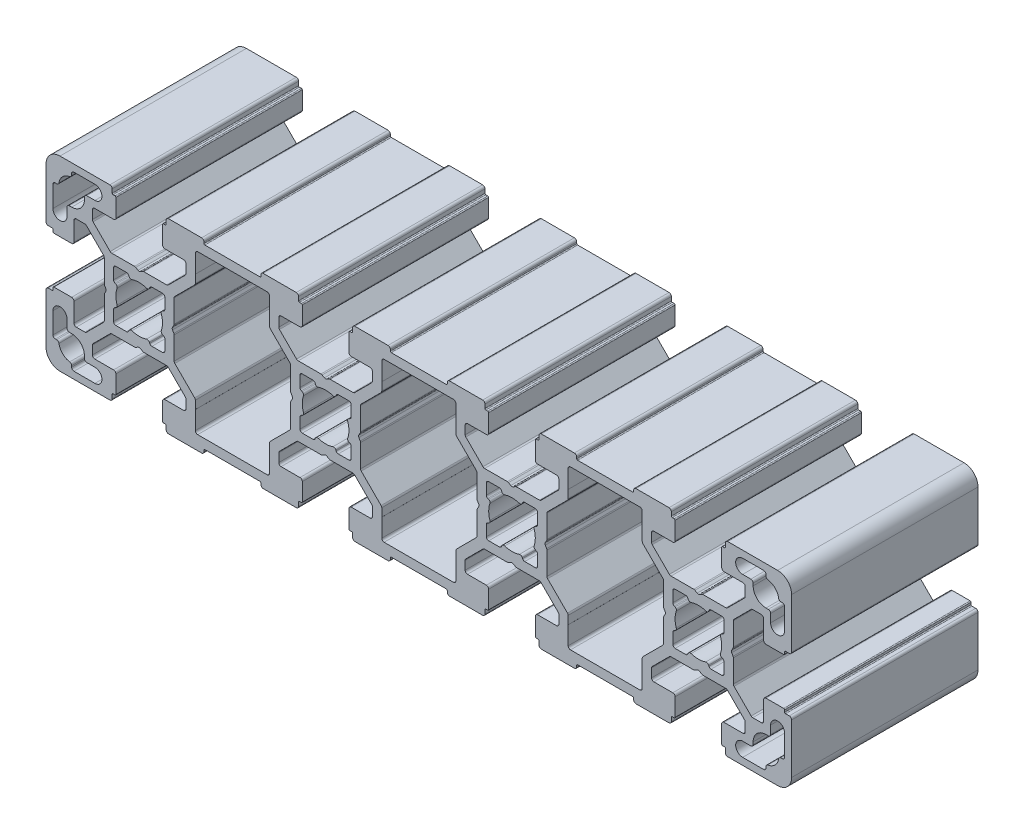
SolidWorks part; units mm, degrees
material "АД31Т ГОСТ 4784-97"
ref_plane "Спереди" through (0, 0, 0) normal (0, 0, 1) x (1, 0, 0)
ref_plane "Сверху" through (0, 0, 0) normal (0, 1, 0) x (1, 0, 0)
ref_plane "Справа" through (0, 0, 0) normal (1, 0, 0) x (0, 0, -1)
sketch "Эскиз1" plane through (0, 0, 0) normal (0, 0, 1) x (1, 0, 0)
  line B0 (-95.6887, 53.3596) -> (-95.6109, 53.5385)
  line B1 (-98.4194, 53.059) -> (-96.1473, 53.059)
  line B2 (-98.9194, 55.8312) -> (-98.9194, 53.559)
  line B3 (-98.4399, 56.3675) -> (-98.6188, 56.2897)
  line B4 (-98.6188, 60.8283) -> (-98.4399, 60.7505)
  line B5 (-98.9194, 63.559) -> (-98.9194, 61.2868)
  line B6 (-96.1473, 64.059) -> (-98.4194, 64.059)
  line B7 (-95.6109, 63.5795) -> (-95.6887, 63.7584)
  line B8 (-91.1502, 63.7584) -> (-91.2279, 63.5795)
  line B9 (-88.4194, 64.059) -> (-90.6916, 64.059)
  line B10 (-87.9194, 61.2868) -> (-87.9194, 63.559)
  line B11 (-88.399, 60.7505) -> (-88.2201, 60.8283)
  line B12 (-88.2201, 56.2897) -> (-88.399, 56.3675)
  line B13 (-87.9194, 53.559) -> (-87.9194, 55.8312)
  line B14 (-90.6916, 53.059) -> (-88.4194, 53.059)
  line B15 (-91.2279, 53.5385) -> (-91.1502, 53.3596)
  line B16 (-65.323, 48.0696) -> (-61.0659, 52.3267)
  line B17 (-65.4694, 45.9733) -> (-65.4694, 47.7161)
  line B18 (-65.4844, 45.9788) -> (-65.4694, 45.9733)
  line B19 (-65.4711, 42.0607) -> (-65.4844, 45.9788)
  line B20 (-80.8677, 41.559) -> (-65.9711, 41.559)
  line B21 (-81.3544, 45.9788) -> (-81.3677, 42.0607)
  line B22 (-81.3694, 45.9733) -> (-81.3544, 45.9788)
  line B23 (-81.3694, 47.7161) -> (-81.3694, 45.9733)
  line B24 (-85.773, 52.3267) -> (-81.5159, 48.0696)
  line B25 (-85.9194, 57.559) -> (-85.9194, 52.6803)
  line B26 (-86.2751, 58.309) -> (-85.9864, 57.809)
  line B27 (-85.9864, 59.309) -> (-86.2751, 58.809)
  line B28 (-85.9194, 64.4377) -> (-85.9194, 59.559)
  line B29 (-81.5159, 69.0483) -> (-85.773, 64.7912)
  line B30 (-81.3694, 71.1446) -> (-81.3694, 69.4019)
  line B31 (-81.3544, 71.1391) -> (-81.3694, 71.1446)
  line B32 (-81.3677, 75.0573) -> (-81.3544, 71.1391)
  line B33 (-65.9711, 75.559) -> (-80.8677, 75.559)
  line B34 (-65.4844, 71.1391) -> (-65.4711, 75.0573)
  line B35 (-65.4694, 71.1446) -> (-65.4844, 71.1391)
  line B36 (-65.4694, 69.4019) -> (-65.4694, 71.1446)
  line B37 (-61.0659, 64.7912) -> (-65.323, 69.0483)
  line B38 (-60.9194, 59.559) -> (-60.9194, 64.4377)
  line B39 (-60.5638, 58.809) -> (-60.8524, 59.309)
  line B40 (-60.8524, 57.809) -> (-60.5638, 58.309)
  line B41 (-60.9194, 52.6803) -> (-60.9194, 57.559)
  line B42 (-55.6887, 53.3596) -> (-55.6109, 53.5385)
  line B43 (-58.4194, 53.059) -> (-56.1473, 53.059)
  line B44 (-58.9194, 55.8312) -> (-58.9194, 53.559)
  line B45 (-58.4399, 56.3675) -> (-58.6188, 56.2897)
  line B46 (-58.6188, 60.8283) -> (-58.4399, 60.7505)
  line B47 (-58.9194, 63.559) -> (-58.9194, 61.2868)
  line B48 (-56.1473, 64.059) -> (-58.4194, 64.059)
  line B49 (-55.6109, 63.5795) -> (-55.6887, 63.7584)
  line B50 (-51.1502, 63.7584) -> (-51.2279, 63.5795)
  line B51 (-48.4194, 64.059) -> (-50.6916, 64.059)
  line B52 (-47.9194, 61.2868) -> (-47.9194, 63.559)
  line B53 (-48.399, 60.7505) -> (-48.2201, 60.8283)
  line B54 (-48.2201, 56.2897) -> (-48.399, 56.3675)
  line B55 (-47.9194, 53.559) -> (-47.9194, 55.8312)
  line B56 (-50.6916, 53.059) -> (-48.4194, 53.059)
  line B57 (-51.2279, 53.5385) -> (-51.1502, 53.3596)
  line B58 (-25.9711, 75.559) -> (-40.8677, 75.559)
  line B59 (-25.4844, 71.1391) -> (-25.4711, 75.0573)
  line B60 (-25.4694, 71.1446) -> (-25.4844, 71.1391)
  line B61 (-25.4694, 69.4019) -> (-25.4694, 71.1446)
  line B62 (-21.0659, 64.7912) -> (-25.323, 69.0483)
  line B63 (-20.9194, 59.559) -> (-20.9194, 64.4377)
  line B64 (-20.5638, 58.809) -> (-20.8524, 59.309)
  line B65 (-20.8524, 57.809) -> (-20.5638, 58.309)
  line B66 (-20.9194, 52.6803) -> (-20.9194, 57.559)
  line B67 (-25.323, 48.0696) -> (-21.0659, 52.3267)
  line B68 (-25.4694, 45.9733) -> (-25.4694, 47.7161)
  line B69 (-25.4844, 45.9788) -> (-25.4694, 45.9733)
  line B70 (-25.4711, 42.0607) -> (-25.4844, 45.9788)
  line B71 (-40.8677, 41.559) -> (-25.9711, 41.559)
  line B72 (-41.3544, 45.9788) -> (-41.3677, 42.0607)
  line B73 (-41.3694, 45.9733) -> (-41.3544, 45.9788)
  line B74 (-41.3694, 47.7161) -> (-41.3694, 45.9733)
  line B75 (-45.773, 52.3267) -> (-41.5159, 48.0696)
  line B76 (-45.9194, 57.559) -> (-45.9194, 52.6803)
  line B77 (-46.2751, 58.309) -> (-45.9864, 57.809)
  line B78 (-45.9864, 59.309) -> (-46.2751, 58.809)
  line B79 (-45.9194, 64.4377) -> (-45.9194, 59.559)
  line B80 (-41.5159, 69.0483) -> (-45.773, 64.7912)
  line B81 (-41.3694, 71.1446) -> (-41.3694, 69.4019)
  line B82 (-41.3544, 71.1391) -> (-41.3694, 71.1446)
  line B83 (-41.3677, 75.0573) -> (-41.3544, 71.1391)
  line B84 (-27.5094, 77.559) -> (-39.3294, 77.559)
  line B85 (-39.5294, 77.759) -> (-39.5294, 78.059)
  line B86 (-40.0294, 78.559) -> (-47.1194, 78.559)
  line B87 (-47.6194, 78.059) -> (-47.6194, 77.259)
  line B88 (-47.8194, 77.059) -> (-48.2194, 77.059)
  line B89 (-48.4194, 76.859) -> (-48.4194, 73.059)
  line B90 (-47.9194, 72.559) -> (-43.8694, 72.559)
  line B91 (-43.3694, 72.059) -> (-43.3694, 70.2303)
  line B92 (-43.5159, 69.8767) -> (-47.1872, 66.2054)
  line B93 (-47.5408, 66.059) -> (-52.4194, 66.059)
  line B94 (-52.6694, 65.992) -> (-53.1694, 65.7033)
  line B95 (-53.6694, 65.7033) -> (-54.1694, 65.992)
  line B96 (-54.4194, 66.059) -> (-59.2981, 66.059)
  line B97 (-59.6517, 66.2054) -> (-63.323, 69.8767)
  line B98 (-63.4694, 70.2303) -> (-63.4694, 72.059)
  line B99 (-62.9694, 72.559) -> (-58.9194, 72.559)
  line B100 (-58.4194, 73.059) -> (-58.4194, 76.859)
  line B101 (-58.6194, 77.059) -> (-59.0194, 77.059)
  line B102 (-59.2194, 77.259) -> (-59.2194, 78.059)
  line B103 (-59.7194, 78.559) -> (-66.8094, 78.559)
  line B104 (-67.3094, 78.059) -> (-67.3094, 77.759)
  line B105 (-67.5094, 77.559) -> (-79.3294, 77.559)
  line B106 (-79.5294, 77.759) -> (-79.5294, 78.059)
  line B107 (-80.0294, 78.559) -> (-87.1194, 78.559)
  line B108 (-87.6194, 78.059) -> (-87.6194, 77.259)
  line B109 (-87.8194, 77.059) -> (-88.2194, 77.059)
  line B110 (-88.4194, 76.859) -> (-88.4194, 73.059)
  line B111 (-87.9194, 72.559) -> (-83.8694, 72.559)
  line B112 (-83.3694, 72.059) -> (-83.3694, 70.2303)
  line B113 (-83.5159, 69.8767) -> (-87.1872, 66.2054)
  line B114 (-87.5408, 66.059) -> (-92.4194, 66.059)
  line B115 (-92.6694, 65.992) -> (-93.1694, 65.7033)
  line B116 (-93.6694, 65.7033) -> (-94.1694, 65.992)
  line B117 (-94.4194, 66.059) -> (-99.2981, 66.059)
  line B118 (-99.6517, 66.2054) -> (-103.323, 69.8767)
  line B119 (-103.4694, 70.2303) -> (-103.4694, 72.059)
  line B120 (-102.9694, 72.559) -> (-98.9194, 72.559)
  line B121 (-98.4194, 73.059) -> (-98.4194, 76.859)
  line B122 (-98.6194, 77.059) -> (-99.0194, 77.059)
  line B123 (-99.2194, 77.259) -> (-99.2194, 78.059)
  line B124 (-99.7194, 78.559) -> (-110.4194, 78.559)
  line B125 (-113.4194, 75.559) -> (-113.4194, 64.859)
  line B126 (-112.9194, 64.359) -> (-112.1194, 64.359)
  line B127 (-111.9194, 64.159) -> (-111.9194, 63.759)
  line B128 (-111.7194, 63.559) -> (-107.9194, 63.559)
  line B129 (-107.4194, 64.059) -> (-107.4194, 68.109)
  line B130 (-106.9194, 68.609) -> (-105.0908, 68.609)
  line B131 (-104.7372, 68.4625) -> (-101.0659, 64.7912)
  line B132 (-100.9194, 64.4377) -> (-100.9194, 59.559)
  line B133 (-100.8524, 59.309) -> (-100.5638, 58.809)
  line B134 (-100.5638, 58.309) -> (-100.8524, 57.809)
  line B135 (-100.9194, 57.559) -> (-100.9194, 52.6803)
  line B136 (-101.0659, 52.3267) -> (-104.7372, 48.6554)
  line B137 (-105.0908, 48.509) -> (-106.9194, 48.509)
  line B138 (-107.4194, 49.009) -> (-107.4194, 53.059)
  line B139 (-107.9194, 53.559) -> (-111.7194, 53.559)
  line B140 (-111.9194, 53.359) -> (-111.9194, 52.959)
  line B141 (-112.1194, 52.759) -> (-112.9194, 52.759)
  line B142 (-113.4194, 52.259) -> (-113.4194, 41.559)
  line B143 (-110.4194, 38.559) -> (-99.7194, 38.559)
  line B144 (-99.2194, 39.059) -> (-99.2194, 39.859)
  line B145 (-99.0194, 40.059) -> (-98.6194, 40.059)
  line B146 (-98.4194, 40.259) -> (-98.4194, 44.059)
  line B147 (-98.9194, 44.559) -> (-102.9694, 44.559)
  line B148 (-103.4694, 45.059) -> (-103.4694, 46.8877)
  line B149 (-103.323, 47.2412) -> (-99.6517, 50.9125)
  line B150 (-99.2981, 51.059) -> (-94.4194, 51.059)
  line B151 (-94.1694, 51.126) -> (-93.6694, 51.4146)
  line B152 (-93.1694, 51.4146) -> (-92.6694, 51.126)
  line B153 (-92.4194, 51.059) -> (-87.5408, 51.059)
  line B154 (-87.1872, 50.9125) -> (-83.5159, 47.2412)
  line B155 (-83.3694, 46.8877) -> (-83.3694, 45.059)
  line B156 (-83.8694, 44.559) -> (-87.9194, 44.559)
  line B157 (-88.4194, 44.059) -> (-88.4194, 40.259)
  line B158 (-88.2194, 40.059) -> (-87.8194, 40.059)
  line B159 (-87.6194, 39.859) -> (-87.6194, 39.059)
  line B160 (-87.1194, 38.559) -> (-80.0294, 38.559)
  line B161 (-79.5294, 39.059) -> (-79.5294, 39.359)
  line B162 (-79.3294, 39.559) -> (-67.5094, 39.559)
  line B163 (-67.3094, 39.359) -> (-67.3094, 39.059)
  line B164 (-66.8094, 38.559) -> (-59.7194, 38.559)
  line B165 (-59.2194, 39.059) -> (-59.2194, 39.859)
  line B166 (-59.0194, 40.059) -> (-58.6194, 40.059)
  line B167 (-58.4194, 40.259) -> (-58.4194, 44.059)
  line B168 (-58.9194, 44.559) -> (-62.9694, 44.559)
  line B169 (-63.4694, 45.059) -> (-63.4694, 46.8877)
  line B170 (-63.323, 47.2412) -> (-59.6517, 50.9125)
  line B171 (-59.2981, 51.059) -> (-54.4194, 51.059)
  line B172 (-54.1694, 51.126) -> (-53.6694, 51.4146)
  line B173 (-53.1694, 51.4146) -> (-52.6694, 51.126)
  line B174 (-52.4194, 51.059) -> (-47.5408, 51.059)
  line B175 (-47.1872, 50.9125) -> (-43.5159, 47.2412)
  line B176 (-43.3694, 46.8877) -> (-43.3694, 45.059)
  line B177 (-43.8694, 44.559) -> (-47.9194, 44.559)
  line B178 (-48.4194, 44.059) -> (-48.4194, 40.259)
  line B179 (-48.2194, 40.059) -> (-47.8194, 40.059)
  line B180 (-47.6194, 39.859) -> (-47.6194, 39.059)
  line B181 (-47.1194, 38.559) -> (-40.0294, 38.559)
  line B182 (-39.5294, 39.059) -> (-39.5294, 39.359)
  line B183 (-39.3294, 39.559) -> (-27.5094, 39.559)
  line B184 (-27.3094, 39.359) -> (-27.3094, 39.059)
  line B185 (-26.8094, 38.559) -> (-19.7194, 38.559)
  line B186 (-19.2194, 39.059) -> (-19.2194, 39.859)
  line B187 (-19.0194, 40.059) -> (-18.6194, 40.059)
  line B188 (-18.4194, 40.259) -> (-18.4194, 44.059)
  line B189 (-18.9194, 44.559) -> (-22.9694, 44.559)
  line B190 (-23.4694, 45.059) -> (-23.4694, 46.8877)
  line B191 (-23.323, 47.2412) -> (-19.6517, 50.9125)
  line B192 (-19.2981, 51.059) -> (-14.4194, 51.059)
  line B193 (-14.1694, 51.126) -> (-13.6694, 51.4146)
  line B194 (-13.1694, 51.4146) -> (-12.6694, 51.126)
  line B195 (-12.4194, 51.059) -> (-7.5408, 51.059)
  line B196 (-7.1872, 50.9125) -> (-3.5159, 47.2412)
  line B197 (-3.3694, 46.8877) -> (-3.3694, 45.059)
  line B198 (-3.8694, 44.559) -> (-7.9194, 44.559)
  line B199 (-8.4194, 44.059) -> (-8.4194, 40.259)
  line B200 (-8.2194, 40.059) -> (-7.8194, 40.059)
  line B201 (-7.6194, 39.859) -> (-7.6194, 39.059)
  line B202 (-7.1194, 38.559) -> (-0.0294, 38.559)
  line B203 (0.4706, 39.059) -> (0.4706, 39.359)
  line B204 (0.6706, 39.559) -> (12.4906, 39.559)
  line B205 (12.6906, 39.359) -> (12.6906, 39.059)
  line B206 (13.1906, 38.559) -> (20.2806, 38.559)
  line B207 (20.7806, 39.059) -> (20.7806, 39.859)
  line B208 (20.9806, 40.059) -> (21.3806, 40.059)
  line B209 (21.5806, 40.259) -> (21.5806, 44.059)
  line B210 (21.0806, 44.559) -> (17.0306, 44.559)
  line B211 (16.5306, 45.059) -> (16.5306, 46.8877)
  line B212 (16.677, 47.2412) -> (20.3483, 50.9125)
  line B213 (20.7019, 51.059) -> (25.5806, 51.059)
  line B214 (25.8306, 51.126) -> (26.3306, 51.4146)
  line B215 (26.8306, 51.4146) -> (27.3306, 51.126)
  line B216 (27.5806, 51.059) -> (32.4592, 51.059)
  line B217 (32.8128, 50.9125) -> (36.4841, 47.2412)
  line B218 (36.6306, 46.8877) -> (36.6306, 45.059)
  line B219 (36.1306, 44.559) -> (32.0806, 44.559)
  line B220 (31.5806, 44.059) -> (31.5806, 40.259)
  line B221 (31.7806, 40.059) -> (32.1806, 40.059)
  line B222 (32.3806, 39.859) -> (32.3806, 39.059)
  line B223 (32.8806, 38.559) -> (43.5806, 38.559)
  line B224 (46.5806, 41.559) -> (46.5806, 52.259)
  line B225 (46.0806, 52.759) -> (45.2806, 52.759)
  line B226 (45.0806, 52.959) -> (45.0806, 53.359)
  line B227 (44.8806, 53.559) -> (41.0806, 53.559)
  line B228 (40.5806, 53.059) -> (40.5806, 49.009)
  line B229 (40.0806, 48.509) -> (38.2519, 48.509)
  line B230 (37.8983, 48.6554) -> (34.227, 52.3267)
  line B231 (34.0806, 52.6803) -> (34.0806, 57.559)
  line B232 (34.0136, 57.809) -> (33.7249, 58.309)
  line B233 (33.7249, 58.809) -> (34.0136, 59.309)
  line B234 (34.0806, 59.559) -> (34.0806, 64.4377)
  line B235 (34.227, 64.7912) -> (37.8983, 68.4625)
  line B236 (38.2519, 68.609) -> (40.0806, 68.609)
  line B237 (40.5806, 68.109) -> (40.5806, 64.059)
  line B238 (41.0806, 63.559) -> (44.8806, 63.559)
  line B239 (45.0806, 63.759) -> (45.0806, 64.159)
  line B240 (45.2806, 64.359) -> (46.0806, 64.359)
  line B241 (46.5806, 64.859) -> (46.5806, 75.559)
  line B242 (43.5806, 78.559) -> (32.8806, 78.559)
  line B243 (32.3806, 78.059) -> (32.3806, 77.259)
  line B244 (32.1806, 77.059) -> (31.7806, 77.059)
  line B245 (31.5806, 76.859) -> (31.5806, 73.059)
  line B246 (32.0806, 72.559) -> (36.1306, 72.559)
  line B247 (36.6306, 72.059) -> (36.6306, 70.2303)
  line B248 (36.4841, 69.8767) -> (32.8128, 66.2054)
  line B249 (32.4592, 66.059) -> (27.5806, 66.059)
  line B250 (27.3306, 65.992) -> (26.8306, 65.7033)
  line B251 (26.3306, 65.7033) -> (25.8306, 65.992)
  line B252 (25.5806, 66.059) -> (20.7019, 66.059)
  line B253 (20.3483, 66.2054) -> (16.677, 69.8767)
  line B254 (16.5306, 70.2303) -> (16.5306, 72.059)
  line B255 (17.0306, 72.559) -> (21.0806, 72.559)
  line B256 (21.5806, 73.059) -> (21.5806, 76.859)
  line B257 (21.3806, 77.059) -> (20.9806, 77.059)
  line B258 (20.7806, 77.259) -> (20.7806, 78.059)
  line B259 (20.2806, 78.559) -> (13.1906, 78.559)
  line B260 (12.6906, 78.059) -> (12.6906, 77.759)
  line B261 (12.4906, 77.559) -> (0.6706, 77.559)
  line B262 (0.4706, 77.759) -> (0.4706, 78.059)
  line B263 (-0.0294, 78.559) -> (-7.1194, 78.559)
  line B264 (-7.6194, 78.059) -> (-7.6194, 77.259)
  line B265 (-7.8194, 77.059) -> (-8.2194, 77.059)
  line B266 (-8.4194, 76.859) -> (-8.4194, 73.059)
  line B267 (-7.9194, 72.559) -> (-3.8694, 72.559)
  line B268 (-3.3694, 72.059) -> (-3.3694, 70.2303)
  line B269 (-3.5159, 69.8767) -> (-7.1872, 66.2054)
  line B270 (-7.5408, 66.059) -> (-12.4194, 66.059)
  line B271 (-12.6694, 65.992) -> (-13.1694, 65.7033)
  line B272 (-13.6694, 65.7033) -> (-14.1694, 65.992)
  line B273 (-14.4194, 66.059) -> (-19.2981, 66.059)
  line B274 (-19.6517, 66.2054) -> (-23.323, 69.8767)
  line B275 (-23.4694, 70.2303) -> (-23.4694, 72.059)
  line B276 (-22.9694, 72.559) -> (-18.9194, 72.559)
  line B277 (-18.4194, 73.059) -> (-18.4194, 76.859)
  line B278 (-18.6194, 77.059) -> (-19.0194, 77.059)
  line B279 (-19.2194, 77.259) -> (-19.2194, 78.059)
  line B280 (-19.7194, 78.559) -> (-26.8094, 78.559)
  line B281 (-27.3094, 78.059) -> (-27.3094, 77.759)
  line B282 (-11.1502, 63.7584) -> (-11.2279, 63.5795)
  line B283 (-8.4194, 64.059) -> (-10.6916, 64.059)
  line B284 (-7.9194, 61.2868) -> (-7.9194, 63.559)
  line B285 (-8.399, 60.7505) -> (-8.2201, 60.8283)
  line B286 (-8.2201, 56.2897) -> (-8.399, 56.3675)
  line B287 (-7.9194, 53.559) -> (-7.9194, 55.8312)
  line B288 (-10.6916, 53.059) -> (-8.4194, 53.059)
  line B289 (-11.2279, 53.5385) -> (-11.1502, 53.3596)
  line B290 (-15.6887, 53.3596) -> (-15.6109, 53.5385)
  line B291 (-18.4194, 53.059) -> (-16.1473, 53.059)
  line B292 (-18.9194, 55.8312) -> (-18.9194, 53.559)
  line B293 (-18.4399, 56.3675) -> (-18.6188, 56.2897)
  line B294 (-18.6188, 60.8283) -> (-18.4399, 60.7505)
  line B295 (-18.9194, 63.559) -> (-18.9194, 61.2868)
  line B296 (-16.1473, 64.059) -> (-18.4194, 64.059)
  line B297 (-15.6109, 63.5795) -> (-15.6887, 63.7584)
  line B298 (14.677, 48.0696) -> (18.9341, 52.3267)
  line B299 (14.5306, 45.9733) -> (14.5306, 47.7161)
  line B300 (14.5156, 45.9788) -> (14.5306, 45.9733)
  line B301 (14.5289, 42.0607) -> (14.5156, 45.9788)
  line B302 (-0.8677, 41.559) -> (14.0289, 41.559)
  line B303 (-1.3544, 45.9788) -> (-1.3677, 42.0607)
  line B304 (-1.3694, 45.9733) -> (-1.3544, 45.9788)
  line B305 (-1.3694, 47.7161) -> (-1.3694, 45.9733)
  line B306 (-5.773, 52.3267) -> (-1.5159, 48.0696)
  line B307 (-5.9194, 57.559) -> (-5.9194, 52.6803)
  line B308 (-6.2751, 58.309) -> (-5.9864, 57.809)
  line B309 (-5.9864, 59.309) -> (-6.2751, 58.809)
  line B310 (-5.9194, 64.4377) -> (-5.9194, 59.559)
  line B311 (-1.5159, 69.0483) -> (-5.773, 64.7912)
  line B312 (-1.3694, 71.1446) -> (-1.3694, 69.4019)
  line B313 (-1.3544, 71.1391) -> (-1.3694, 71.1446)
  line B314 (-1.3677, 75.0573) -> (-1.3544, 71.1391)
  line B315 (14.0289, 75.559) -> (-0.8677, 75.559)
  line B316 (14.5156, 71.1391) -> (14.5289, 75.0573)
  line B317 (14.5306, 71.1446) -> (14.5156, 71.1391)
  line B318 (14.5306, 69.4019) -> (14.5306, 71.1446)
  line B319 (18.9341, 64.7912) -> (14.677, 69.0483)
  line B320 (19.0806, 59.559) -> (19.0806, 64.4377)
  line B321 (19.4362, 58.809) -> (19.1476, 59.309)
  line B322 (19.1476, 57.809) -> (19.4362, 58.309)
  line B323 (19.0806, 52.6803) -> (19.0806, 57.559)
  line B324 (31.7799, 56.2897) -> (31.601, 56.3675)
  line B325 (32.0806, 53.559) -> (32.0806, 55.8312)
  line B326 (29.3084, 53.059) -> (31.5806, 53.059)
  line B327 (28.7721, 53.5385) -> (28.8498, 53.3596)
  line B328 (24.3113, 53.3596) -> (24.3891, 53.5385)
  line B329 (21.5806, 53.059) -> (23.8527, 53.059)
  line B330 (21.0806, 55.8312) -> (21.0806, 53.559)
  line B331 (21.5601, 56.3675) -> (21.3812, 56.2897)
  line B332 (21.3812, 60.8283) -> (21.5601, 60.7505)
  line B333 (21.0806, 63.559) -> (21.0806, 61.2868)
  line B334 (23.8527, 64.059) -> (21.5806, 64.059)
  line B335 (24.3891, 63.5795) -> (24.3113, 63.7584)
  line B336 (28.8498, 63.7584) -> (28.7721, 63.5795)
  line B337 (31.5806, 64.059) -> (29.3084, 64.059)
  line B338 (32.0806, 61.2868) -> (32.0806, 63.559)
  line B339 (31.601, 60.7505) -> (31.7799, 60.8283)
  line B340 (44.5806, 73.059) -> (44.2919, 73.059)
  line B341 (45.0806, 68.059) -> (45.0806, 72.559)
  line B342 (42.0806, 69.809) -> (42.0806, 68.059)
  line B343 (41.0806, 70.309) -> (41.5806, 70.309)
  line B344 (38.3306, 73.559) -> (38.3306, 73.059)
  line B345 (36.0806, 74.059) -> (37.8306, 74.059)
  line B346 (40.5806, 77.059) -> (36.0806, 77.059)
  line B347 (41.0806, 76.2703) -> (41.0806, 76.559)
  line B348 (44.2919, 44.059) -> (44.5806, 44.059)
  line B349 (41.0806, 40.559) -> (41.0806, 40.8477)
  line B350 (36.0806, 40.059) -> (40.5806, 40.059)
  line B351 (37.8306, 43.059) -> (36.0806, 43.059)
  line B352 (38.3306, 44.059) -> (38.3306, 43.559)
  line B353 (41.5806, 46.809) -> (41.0806, 46.809)
  line B354 (42.0806, 49.059) -> (42.0806, 47.309)
  line B355 (45.0806, 44.559) -> (45.0806, 49.059)
  line B356 (-111.4194, 44.059) -> (-111.1307, 44.059)
  line B357 (-111.9194, 49.059) -> (-111.9194, 44.559)
  line B358 (-108.9194, 47.309) -> (-108.9194, 49.059)
  line B359 (-107.9194, 46.809) -> (-108.4194, 46.809)
  line B360 (-105.1694, 43.559) -> (-105.1694, 44.059)
  line B361 (-102.9194, 43.059) -> (-104.6694, 43.059)
  line B362 (-107.4194, 40.059) -> (-102.9194, 40.059)
  line B363 (-107.9194, 40.8477) -> (-107.9194, 40.559)
  line B364 (-111.1307, 73.059) -> (-111.4194, 73.059)
  line B365 (-107.9194, 76.559) -> (-107.9194, 76.2703)
  line B366 (-102.9194, 77.059) -> (-107.4194, 77.059)
  line B367 (-104.6694, 74.059) -> (-102.9194, 74.059)
  line B368 (-105.1694, 73.059) -> (-105.1694, 73.559)
  line B369 (-108.4194, 70.309) -> (-107.9194, 70.309)
  line B370 (-108.9194, 68.059) -> (-108.9194, 69.809)
  line B371 (-111.9194, 72.559) -> (-111.9194, 68.059)
  arc B372 (-94.9949, 53.8137) -> (-91.844, 53.8137) centre (-93.4194, 58.559) ccw
  arc B373 (-94.9949, 53.8137) -> (-95.6109, 53.5385) centre (-95.1524, 53.3391) ccw
  arc B374 (-96.1473, 53.059) -> (-95.6887, 53.3596) centre (-96.1473, 53.559) ccw
  arc B375 (-98.9194, 53.559) -> (-98.4194, 53.059) centre (-98.4194, 53.559) ccw
  arc B376 (-98.6188, 56.2897) -> (-98.9194, 55.8312) centre (-98.4194, 55.8312) ccw
  arc B377 (-98.4399, 56.3675) -> (-98.1648, 56.9836) centre (-98.6393, 56.826) ccw
  arc B378 (-98.1648, 60.1344) -> (-98.1648, 56.9836) centre (-93.4194, 58.559) ccw
  arc B379 (-98.1648, 60.1344) -> (-98.4399, 60.7505) centre (-98.6393, 60.2919) ccw
  arc B380 (-98.9194, 61.2868) -> (-98.6188, 60.8283) centre (-98.4194, 61.2868) ccw
  arc B381 (-98.4194, 64.059) -> (-98.9194, 63.559) centre (-98.4194, 63.559) ccw
  arc B382 (-95.6887, 63.7584) -> (-96.1473, 64.059) centre (-96.1473, 63.559) ccw
  arc B383 (-95.6109, 63.5795) -> (-94.9949, 63.3043) centre (-95.1524, 63.7788) ccw
  arc B384 (-91.844, 63.3043) -> (-94.9949, 63.3043) centre (-93.4194, 58.559) ccw
  arc B385 (-91.844, 63.3043) -> (-91.2279, 63.5795) centre (-91.6865, 63.7788) ccw
  arc B386 (-90.6916, 64.059) -> (-91.1502, 63.7584) centre (-90.6916, 63.559) ccw
  arc B387 (-87.9194, 63.559) -> (-88.4194, 64.059) centre (-88.4194, 63.559) ccw
  arc B388 (-88.2201, 60.8283) -> (-87.9194, 61.2868) centre (-88.4194, 61.2868) ccw
  arc B389 (-88.399, 60.7505) -> (-88.6741, 60.1344) centre (-88.1996, 60.2919) ccw
  arc B390 (-88.6741, 56.9836) -> (-88.6741, 60.1344) centre (-93.4194, 58.559) ccw
  arc B391 (-88.6741, 56.9836) -> (-88.399, 56.3675) centre (-88.1996, 56.826) ccw
  arc B392 (-87.9194, 55.8312) -> (-88.2201, 56.2897) centre (-88.4194, 55.8312) ccw
  arc B393 (-88.4194, 53.059) -> (-87.9194, 53.559) centre (-88.4194, 53.559) ccw
  arc B394 (-91.1502, 53.3596) -> (-90.6916, 53.059) centre (-90.6916, 53.559) ccw
  arc B395 (-91.2279, 53.5385) -> (-91.844, 53.8137) centre (-91.6865, 53.3391) ccw
  arc B396 (-65.323, 48.0696) -> (-65.4694, 47.7161) centre (-64.9694, 47.7161) ccw
  arc B397 (-65.9711, 41.559) -> (-65.4711, 42.0607) centre (-65.9711, 42.059) ccw
  arc B398 (-81.3677, 42.0607) -> (-80.8677, 41.559) centre (-80.8677, 42.059) ccw
  arc B399 (-81.3694, 47.7161) -> (-81.5159, 48.0696) centre (-81.8694, 47.7161) ccw
  arc B400 (-85.9194, 52.6803) -> (-85.773, 52.3267) centre (-85.4194, 52.6803) ccw
  arc B401 (-85.9194, 57.559) -> (-85.9864, 57.809) centre (-86.4194, 57.559) ccw
  arc B402 (-86.2751, 58.809) -> (-86.2751, 58.309) centre (-85.8421, 58.559) ccw
  arc B403 (-85.9864, 59.309) -> (-85.9194, 59.559) centre (-86.4194, 59.559) ccw
  arc B404 (-85.773, 64.7912) -> (-85.9194, 64.4377) centre (-85.4194, 64.4377) ccw
  arc B405 (-81.5159, 69.0483) -> (-81.3694, 69.4019) centre (-81.8694, 69.4019) ccw
  arc B406 (-80.8677, 75.559) -> (-81.3677, 75.0573) centre (-80.8677, 75.059) ccw
  arc B407 (-65.4711, 75.0573) -> (-65.9711, 75.559) centre (-65.9711, 75.059) ccw
  arc B408 (-65.4694, 69.4019) -> (-65.323, 69.0483) centre (-64.9694, 69.4019) ccw
  arc B409 (-60.9194, 64.4377) -> (-61.0659, 64.7912) centre (-61.4194, 64.4377) ccw
  arc B410 (-60.9194, 59.559) -> (-60.8524, 59.309) centre (-60.4194, 59.559) ccw
  arc B411 (-60.5638, 58.309) -> (-60.5638, 58.809) centre (-60.9968, 58.559) ccw
  arc B412 (-60.8524, 57.809) -> (-60.9194, 57.559) centre (-60.4194, 57.559) ccw
  arc B413 (-61.0659, 52.3267) -> (-60.9194, 52.6803) centre (-61.4194, 52.6803) ccw
  arc B414 (-54.9949, 53.8137) -> (-51.844, 53.8137) centre (-53.4194, 58.559) ccw
  arc B415 (-54.9949, 53.8137) -> (-55.6109, 53.5385) centre (-55.1524, 53.3391) ccw
  arc B416 (-56.1473, 53.059) -> (-55.6887, 53.3596) centre (-56.1473, 53.559) ccw
  arc B417 (-58.9194, 53.559) -> (-58.4194, 53.059) centre (-58.4194, 53.559) ccw
  arc B418 (-58.6188, 56.2897) -> (-58.9194, 55.8312) centre (-58.4194, 55.8312) ccw
  arc B419 (-58.4399, 56.3675) -> (-58.1648, 56.9836) centre (-58.6393, 56.826) ccw
  arc B420 (-58.1648, 60.1344) -> (-58.1648, 56.9836) centre (-53.4194, 58.559) ccw
  arc B421 (-58.1648, 60.1344) -> (-58.4399, 60.7505) centre (-58.6393, 60.2919) ccw
  arc B422 (-58.9194, 61.2868) -> (-58.6188, 60.8283) centre (-58.4194, 61.2868) ccw
  arc B423 (-58.4194, 64.059) -> (-58.9194, 63.559) centre (-58.4194, 63.559) ccw
  arc B424 (-55.6887, 63.7584) -> (-56.1473, 64.059) centre (-56.1473, 63.559) ccw
  arc B425 (-55.6109, 63.5795) -> (-54.9949, 63.3043) centre (-55.1524, 63.7788) ccw
  arc B426 (-51.844, 63.3043) -> (-54.9949, 63.3043) centre (-53.4194, 58.559) ccw
  arc B427 (-51.844, 63.3043) -> (-51.2279, 63.5795) centre (-51.6865, 63.7788) ccw
  arc B428 (-50.6916, 64.059) -> (-51.1502, 63.7584) centre (-50.6916, 63.559) ccw
  arc B429 (-47.9194, 63.559) -> (-48.4194, 64.059) centre (-48.4194, 63.559) ccw
  arc B430 (-48.2201, 60.8283) -> (-47.9194, 61.2868) centre (-48.4194, 61.2868) ccw
  arc B431 (-48.399, 60.7505) -> (-48.6741, 60.1344) centre (-48.1996, 60.2919) ccw
  arc B432 (-48.6741, 56.9836) -> (-48.6741, 60.1344) centre (-53.4194, 58.559) ccw
  arc B433 (-48.6741, 56.9836) -> (-48.399, 56.3675) centre (-48.1996, 56.826) ccw
  arc B434 (-47.9194, 55.8312) -> (-48.2201, 56.2897) centre (-48.4194, 55.8312) ccw
  arc B435 (-48.4194, 53.059) -> (-47.9194, 53.559) centre (-48.4194, 53.559) ccw
  arc B436 (-51.1502, 53.3596) -> (-50.6916, 53.059) centre (-50.6916, 53.559) ccw
  arc B437 (-51.2279, 53.5385) -> (-51.844, 53.8137) centre (-51.6865, 53.3391) ccw
  arc B438 (-40.8677, 75.559) -> (-41.3677, 75.0573) centre (-40.8677, 75.059) ccw
  arc B439 (-25.4711, 75.0573) -> (-25.9711, 75.559) centre (-25.9711, 75.059) ccw
  arc B440 (-25.4694, 69.4019) -> (-25.323, 69.0483) centre (-24.9694, 69.4019) ccw
  arc B441 (-20.9194, 64.4377) -> (-21.0659, 64.7912) centre (-21.4194, 64.4377) ccw
  arc B442 (-20.9194, 59.559) -> (-20.8524, 59.309) centre (-20.4194, 59.559) ccw
  arc B443 (-20.5638, 58.309) -> (-20.5638, 58.809) centre (-20.9968, 58.559) ccw
  arc B444 (-20.8524, 57.809) -> (-20.9194, 57.559) centre (-20.4194, 57.559) ccw
  arc B445 (-21.0659, 52.3267) -> (-20.9194, 52.6803) centre (-21.4194, 52.6803) ccw
  arc B446 (-25.323, 48.0696) -> (-25.4694, 47.7161) centre (-24.9694, 47.7161) ccw
  arc B447 (-25.9711, 41.559) -> (-25.4711, 42.0607) centre (-25.9711, 42.059) ccw
  arc B448 (-41.3677, 42.0607) -> (-40.8677, 41.559) centre (-40.8677, 42.059) ccw
  arc B449 (-41.3694, 47.7161) -> (-41.5159, 48.0696) centre (-41.8694, 47.7161) ccw
  arc B450 (-45.9194, 52.6803) -> (-45.773, 52.3267) centre (-45.4194, 52.6803) ccw
  arc B451 (-45.9194, 57.559) -> (-45.9864, 57.809) centre (-46.4194, 57.559) ccw
  arc B452 (-46.2751, 58.809) -> (-46.2751, 58.309) centre (-45.8421, 58.559) ccw
  arc B453 (-45.9864, 59.309) -> (-45.9194, 59.559) centre (-46.4194, 59.559) ccw
  arc B454 (-45.773, 64.7912) -> (-45.9194, 64.4377) centre (-45.4194, 64.4377) ccw
  arc B455 (-41.5159, 69.0483) -> (-41.3694, 69.4019) centre (-41.8694, 69.4019) ccw
  arc B456 (-39.5294, 77.759) -> (-39.3294, 77.559) centre (-39.3294, 77.759) ccw
  arc B457 (-39.5294, 78.059) -> (-40.0294, 78.559) centre (-40.0294, 78.059) ccw
  arc B458 (-47.1194, 78.559) -> (-47.6194, 78.059) centre (-47.1194, 78.059) ccw
  arc B459 (-47.8194, 77.059) -> (-47.6194, 77.259) centre (-47.8194, 77.259) ccw
  arc B460 (-48.2194, 77.059) -> (-48.4194, 76.859) centre (-48.2194, 76.859) ccw
  arc B461 (-48.4194, 73.059) -> (-47.9194, 72.559) centre (-47.9194, 73.059) ccw
  arc B462 (-43.3694, 72.059) -> (-43.8694, 72.559) centre (-43.8694, 72.059) ccw
  arc B463 (-43.5159, 69.8767) -> (-43.3694, 70.2303) centre (-43.8694, 70.2303) ccw
  arc B464 (-47.5408, 66.059) -> (-47.1872, 66.2054) centre (-47.5408, 66.559) ccw
  arc B465 (-52.4194, 66.059) -> (-52.6694, 65.992) centre (-52.4194, 65.559) ccw
  arc B466 (-53.6694, 65.7033) -> (-53.1694, 65.7033) centre (-53.4194, 66.1363) ccw
  arc B467 (-54.1694, 65.992) -> (-54.4194, 66.059) centre (-54.4194, 65.559) ccw
  arc B468 (-59.6517, 66.2054) -> (-59.2981, 66.059) centre (-59.2981, 66.559) ccw
  arc B469 (-63.4694, 70.2303) -> (-63.323, 69.8767) centre (-62.9694, 70.2303) ccw
  arc B470 (-62.9694, 72.559) -> (-63.4694, 72.059) centre (-62.9694, 72.059) ccw
  arc B471 (-58.9194, 72.559) -> (-58.4194, 73.059) centre (-58.9194, 73.059) ccw
  arc B472 (-58.4194, 76.859) -> (-58.6194, 77.059) centre (-58.6194, 76.859) ccw
  arc B473 (-59.2194, 77.259) -> (-59.0194, 77.059) centre (-59.0194, 77.259) ccw
  arc B474 (-59.2194, 78.059) -> (-59.7194, 78.559) centre (-59.7194, 78.059) ccw
  arc B475 (-66.8094, 78.559) -> (-67.3094, 78.059) centre (-66.8094, 78.059) ccw
  arc B476 (-67.5094, 77.559) -> (-67.3094, 77.759) centre (-67.5094, 77.759) ccw
  arc B477 (-79.5294, 77.759) -> (-79.3294, 77.559) centre (-79.3294, 77.759) ccw
  arc B478 (-79.5294, 78.059) -> (-80.0294, 78.559) centre (-80.0294, 78.059) ccw
  arc B479 (-87.1194, 78.559) -> (-87.6194, 78.059) centre (-87.1194, 78.059) ccw
  arc B480 (-87.8194, 77.059) -> (-87.6194, 77.259) centre (-87.8194, 77.259) ccw
  arc B481 (-88.2194, 77.059) -> (-88.4194, 76.859) centre (-88.2194, 76.859) ccw
  arc B482 (-88.4194, 73.059) -> (-87.9194, 72.559) centre (-87.9194, 73.059) ccw
  arc B483 (-83.3694, 72.059) -> (-83.8694, 72.559) centre (-83.8694, 72.059) ccw
  arc B484 (-83.5159, 69.8767) -> (-83.3694, 70.2303) centre (-83.8694, 70.2303) ccw
  arc B485 (-87.5408, 66.059) -> (-87.1872, 66.2054) centre (-87.5408, 66.559) ccw
  arc B486 (-92.4194, 66.059) -> (-92.6694, 65.992) centre (-92.4194, 65.559) ccw
  arc B487 (-93.6694, 65.7033) -> (-93.1694, 65.7033) centre (-93.4194, 66.1363) ccw
  arc B488 (-94.1694, 65.992) -> (-94.4194, 66.059) centre (-94.4194, 65.559) ccw
  arc B489 (-99.6517, 66.2054) -> (-99.2981, 66.059) centre (-99.2981, 66.559) ccw
  arc B490 (-103.4694, 70.2303) -> (-103.323, 69.8767) centre (-102.9694, 70.2303) ccw
  arc B491 (-102.9694, 72.559) -> (-103.4694, 72.059) centre (-102.9694, 72.059) ccw
  arc B492 (-98.9194, 72.559) -> (-98.4194, 73.059) centre (-98.9194, 73.059) ccw
  arc B493 (-98.4194, 76.859) -> (-98.6194, 77.059) centre (-98.6194, 76.859) ccw
  arc B494 (-99.2194, 77.259) -> (-99.0194, 77.059) centre (-99.0194, 77.259) ccw
  arc B495 (-99.2194, 78.059) -> (-99.7194, 78.559) centre (-99.7194, 78.059) ccw
  arc B496 (-110.4194, 78.559) -> (-113.4194, 75.559) centre (-110.4194, 75.559) ccw
  arc B497 (-113.4194, 64.859) -> (-112.9194, 64.359) centre (-112.9194, 64.859) ccw
  arc B498 (-111.9194, 64.159) -> (-112.1194, 64.359) centre (-112.1194, 64.159) ccw
  arc B499 (-111.9194, 63.759) -> (-111.7194, 63.559) centre (-111.7194, 63.759) ccw
  arc B500 (-107.9194, 63.559) -> (-107.4194, 64.059) centre (-107.9194, 64.059) ccw
  arc B501 (-106.9194, 68.609) -> (-107.4194, 68.109) centre (-106.9194, 68.109) ccw
  arc B502 (-104.7372, 68.4625) -> (-105.0908, 68.609) centre (-105.0908, 68.109) ccw
  arc B503 (-100.9194, 64.4377) -> (-101.0659, 64.7912) centre (-101.4194, 64.4377) ccw
  arc B504 (-100.9194, 59.559) -> (-100.8524, 59.309) centre (-100.4194, 59.559) ccw
  arc B505 (-100.5638, 58.309) -> (-100.5638, 58.809) centre (-100.9968, 58.559) ccw
  arc B506 (-100.8524, 57.809) -> (-100.9194, 57.559) centre (-100.4194, 57.559) ccw
  arc B507 (-101.0659, 52.3267) -> (-100.9194, 52.6803) centre (-101.4194, 52.6803) ccw
  arc B508 (-105.0908, 48.509) -> (-104.7372, 48.6554) centre (-105.0908, 49.009) ccw
  arc B509 (-107.4194, 49.009) -> (-106.9194, 48.509) centre (-106.9194, 49.009) ccw
  arc B510 (-107.4194, 53.059) -> (-107.9194, 53.559) centre (-107.9194, 53.059) ccw
  arc B511 (-111.7194, 53.559) -> (-111.9194, 53.359) centre (-111.7194, 53.359) ccw
  arc B512 (-112.1194, 52.759) -> (-111.9194, 52.959) centre (-112.1194, 52.959) ccw
  arc B513 (-112.9194, 52.759) -> (-113.4194, 52.259) centre (-112.9194, 52.259) ccw
  arc B514 (-113.4194, 41.559) -> (-110.4194, 38.559) centre (-110.4194, 41.559) ccw
  arc B515 (-99.7194, 38.559) -> (-99.2194, 39.059) centre (-99.7194, 39.059) ccw
  arc B516 (-99.0194, 40.059) -> (-99.2194, 39.859) centre (-99.0194, 39.859) ccw
  arc B517 (-98.6194, 40.059) -> (-98.4194, 40.259) centre (-98.6194, 40.259) ccw
  arc B518 (-98.4194, 44.059) -> (-98.9194, 44.559) centre (-98.9194, 44.059) ccw
  arc B519 (-103.4694, 45.059) -> (-102.9694, 44.559) centre (-102.9694, 45.059) ccw
  arc B520 (-103.323, 47.2412) -> (-103.4694, 46.8877) centre (-102.9694, 46.8877) ccw
  arc B521 (-99.2981, 51.059) -> (-99.6517, 50.9125) centre (-99.2981, 50.559) ccw
  arc B522 (-94.4194, 51.059) -> (-94.1694, 51.126) centre (-94.4194, 51.559) ccw
  arc B523 (-93.1694, 51.4146) -> (-93.6694, 51.4146) centre (-93.4194, 50.9816) ccw
  arc B524 (-92.6694, 51.126) -> (-92.4194, 51.059) centre (-92.4194, 51.559) ccw
  arc B525 (-87.1872, 50.9125) -> (-87.5408, 51.059) centre (-87.5408, 50.559) ccw
  arc B526 (-83.3694, 46.8877) -> (-83.5159, 47.2412) centre (-83.8694, 46.8877) ccw
  arc B527 (-83.8694, 44.559) -> (-83.3694, 45.059) centre (-83.8694, 45.059) ccw
  arc B528 (-87.9194, 44.559) -> (-88.4194, 44.059) centre (-87.9194, 44.059) ccw
  arc B529 (-88.4194, 40.259) -> (-88.2194, 40.059) centre (-88.2194, 40.259) ccw
  arc B530 (-87.6194, 39.859) -> (-87.8194, 40.059) centre (-87.8194, 39.859) ccw
  arc B531 (-87.6194, 39.059) -> (-87.1194, 38.559) centre (-87.1194, 39.059) ccw
  arc B532 (-80.0294, 38.559) -> (-79.5294, 39.059) centre (-80.0294, 39.059) ccw
  arc B533 (-79.3294, 39.559) -> (-79.5294, 39.359) centre (-79.3294, 39.359) ccw
  arc B534 (-67.3094, 39.359) -> (-67.5094, 39.559) centre (-67.5094, 39.359) ccw
  arc B535 (-67.3094, 39.059) -> (-66.8094, 38.559) centre (-66.8094, 39.059) ccw
  arc B536 (-59.7194, 38.559) -> (-59.2194, 39.059) centre (-59.7194, 39.059) ccw
  arc B537 (-59.0194, 40.059) -> (-59.2194, 39.859) centre (-59.0194, 39.859) ccw
  arc B538 (-58.6194, 40.059) -> (-58.4194, 40.259) centre (-58.6194, 40.259) ccw
  arc B539 (-58.4194, 44.059) -> (-58.9194, 44.559) centre (-58.9194, 44.059) ccw
  arc B540 (-63.4694, 45.059) -> (-62.9694, 44.559) centre (-62.9694, 45.059) ccw
  arc B541 (-63.323, 47.2412) -> (-63.4694, 46.8877) centre (-62.9694, 46.8877) ccw
  arc B542 (-59.2981, 51.059) -> (-59.6517, 50.9125) centre (-59.2981, 50.559) ccw
  arc B543 (-54.4194, 51.059) -> (-54.1694, 51.126) centre (-54.4194, 51.559) ccw
  arc B544 (-53.1694, 51.4146) -> (-53.6694, 51.4146) centre (-53.4194, 50.9816) ccw
  arc B545 (-52.6694, 51.126) -> (-52.4194, 51.059) centre (-52.4194, 51.559) ccw
  arc B546 (-47.1872, 50.9125) -> (-47.5408, 51.059) centre (-47.5408, 50.559) ccw
  arc B547 (-43.3694, 46.8877) -> (-43.5159, 47.2412) centre (-43.8694, 46.8877) ccw
  arc B548 (-43.8694, 44.559) -> (-43.3694, 45.059) centre (-43.8694, 45.059) ccw
  arc B549 (-47.9194, 44.559) -> (-48.4194, 44.059) centre (-47.9194, 44.059) ccw
  arc B550 (-48.4194, 40.259) -> (-48.2194, 40.059) centre (-48.2194, 40.259) ccw
  arc B551 (-47.6194, 39.859) -> (-47.8194, 40.059) centre (-47.8194, 39.859) ccw
  arc B552 (-47.6194, 39.059) -> (-47.1194, 38.559) centre (-47.1194, 39.059) ccw
  arc B553 (-40.0294, 38.559) -> (-39.5294, 39.059) centre (-40.0294, 39.059) ccw
  arc B554 (-39.3294, 39.559) -> (-39.5294, 39.359) centre (-39.3294, 39.359) ccw
  arc B555 (-27.3094, 39.359) -> (-27.5094, 39.559) centre (-27.5094, 39.359) ccw
  arc B556 (-27.3094, 39.059) -> (-26.8094, 38.559) centre (-26.8094, 39.059) ccw
  arc B557 (-19.7194, 38.559) -> (-19.2194, 39.059) centre (-19.7194, 39.059) ccw
  arc B558 (-19.0194, 40.059) -> (-19.2194, 39.859) centre (-19.0194, 39.859) ccw
  arc B559 (-18.6194, 40.059) -> (-18.4194, 40.259) centre (-18.6194, 40.259) ccw
  arc B560 (-18.4194, 44.059) -> (-18.9194, 44.559) centre (-18.9194, 44.059) ccw
  arc B561 (-23.4694, 45.059) -> (-22.9694, 44.559) centre (-22.9694, 45.059) ccw
  arc B562 (-23.323, 47.2412) -> (-23.4694, 46.8877) centre (-22.9694, 46.8877) ccw
  arc B563 (-19.2981, 51.059) -> (-19.6517, 50.9125) centre (-19.2981, 50.559) ccw
  arc B564 (-14.4194, 51.059) -> (-14.1694, 51.126) centre (-14.4194, 51.559) ccw
  arc B565 (-13.1694, 51.4146) -> (-13.6694, 51.4146) centre (-13.4194, 50.9816) ccw
  arc B566 (-12.6694, 51.126) -> (-12.4194, 51.059) centre (-12.4194, 51.559) ccw
  arc B567 (-7.1872, 50.9125) -> (-7.5408, 51.059) centre (-7.5408, 50.559) ccw
  arc B568 (-3.3694, 46.8877) -> (-3.5159, 47.2412) centre (-3.8694, 46.8877) ccw
  arc B569 (-3.8694, 44.559) -> (-3.3694, 45.059) centre (-3.8694, 45.059) ccw
  arc B570 (-7.9194, 44.559) -> (-8.4194, 44.059) centre (-7.9194, 44.059) ccw
  arc B571 (-8.4194, 40.259) -> (-8.2194, 40.059) centre (-8.2194, 40.259) ccw
  arc B572 (-7.6194, 39.859) -> (-7.8194, 40.059) centre (-7.8194, 39.859) ccw
  arc B573 (-7.6194, 39.059) -> (-7.1194, 38.559) centre (-7.1194, 39.059) ccw
  arc B574 (-0.0294, 38.559) -> (0.4706, 39.059) centre (-0.0294, 39.059) ccw
  arc B575 (0.6706, 39.559) -> (0.4706, 39.359) centre (0.6706, 39.359) ccw
  arc B576 (12.6906, 39.359) -> (12.4906, 39.559) centre (12.4906, 39.359) ccw
  arc B577 (12.6906, 39.059) -> (13.1906, 38.559) centre (13.1906, 39.059) ccw
  arc B578 (20.2806, 38.559) -> (20.7806, 39.059) centre (20.2806, 39.059) ccw
  arc B579 (20.9806, 40.059) -> (20.7806, 39.859) centre (20.9806, 39.859) ccw
  arc B580 (21.3806, 40.059) -> (21.5806, 40.259) centre (21.3806, 40.259) ccw
  arc B581 (21.5806, 44.059) -> (21.0806, 44.559) centre (21.0806, 44.059) ccw
  arc B582 (16.5306, 45.059) -> (17.0306, 44.559) centre (17.0306, 45.059) ccw
  arc B583 (16.677, 47.2412) -> (16.5306, 46.8877) centre (17.0306, 46.8877) ccw
  arc B584 (20.7019, 51.059) -> (20.3483, 50.9125) centre (20.7019, 50.559) ccw
  arc B585 (25.5806, 51.059) -> (25.8306, 51.126) centre (25.5806, 51.559) ccw
  arc B586 (26.8306, 51.4146) -> (26.3306, 51.4146) centre (26.5806, 50.9816) ccw
  arc B587 (27.3306, 51.126) -> (27.5806, 51.059) centre (27.5806, 51.559) ccw
  arc B588 (32.8128, 50.9125) -> (32.4592, 51.059) centre (32.4592, 50.559) ccw
  arc B589 (36.6306, 46.8877) -> (36.4841, 47.2412) centre (36.1306, 46.8877) ccw
  arc B590 (36.1306, 44.559) -> (36.6306, 45.059) centre (36.1306, 45.059) ccw
  arc B591 (32.0806, 44.559) -> (31.5806, 44.059) centre (32.0806, 44.059) ccw
  arc B592 (31.5806, 40.259) -> (31.7806, 40.059) centre (31.7806, 40.259) ccw
  arc B593 (32.3806, 39.859) -> (32.1806, 40.059) centre (32.1806, 39.859) ccw
  arc B594 (32.3806, 39.059) -> (32.8806, 38.559) centre (32.8806, 39.059) ccw
  arc B595 (43.5806, 38.559) -> (46.5806, 41.559) centre (43.5806, 41.559) ccw
  arc B596 (46.5806, 52.259) -> (46.0806, 52.759) centre (46.0806, 52.259) ccw
  arc B597 (45.0806, 52.959) -> (45.2806, 52.759) centre (45.2806, 52.959) ccw
  arc B598 (45.0806, 53.359) -> (44.8806, 53.559) centre (44.8806, 53.359) ccw
  arc B599 (41.0806, 53.559) -> (40.5806, 53.059) centre (41.0806, 53.059) ccw
  arc B600 (40.0806, 48.509) -> (40.5806, 49.009) centre (40.0806, 49.009) ccw
  arc B601 (37.8983, 48.6554) -> (38.2519, 48.509) centre (38.2519, 49.009) ccw
  arc B602 (34.0806, 52.6803) -> (34.227, 52.3267) centre (34.5806, 52.6803) ccw
  arc B603 (34.0806, 57.559) -> (34.0136, 57.809) centre (33.5806, 57.559) ccw
  arc B604 (33.7249, 58.809) -> (33.7249, 58.309) centre (34.1579, 58.559) ccw
  arc B605 (34.0136, 59.309) -> (34.0806, 59.559) centre (33.5806, 59.559) ccw
  arc B606 (34.227, 64.7912) -> (34.0806, 64.4377) centre (34.5806, 64.4377) ccw
  arc B607 (38.2519, 68.609) -> (37.8983, 68.4625) centre (38.2519, 68.109) ccw
  arc B608 (40.5806, 68.109) -> (40.0806, 68.609) centre (40.0806, 68.109) ccw
  arc B609 (40.5806, 64.059) -> (41.0806, 63.559) centre (41.0806, 64.059) ccw
  arc B610 (44.8806, 63.559) -> (45.0806, 63.759) centre (44.8806, 63.759) ccw
  arc B611 (45.2806, 64.359) -> (45.0806, 64.159) centre (45.2806, 64.159) ccw
  arc B612 (46.0806, 64.359) -> (46.5806, 64.859) centre (46.0806, 64.859) ccw
  arc B613 (46.5806, 75.559) -> (43.5806, 78.559) centre (43.5806, 75.559) ccw
  arc B614 (32.8806, 78.559) -> (32.3806, 78.059) centre (32.8806, 78.059) ccw
  arc B615 (32.1806, 77.059) -> (32.3806, 77.259) centre (32.1806, 77.259) ccw
  arc B616 (31.7806, 77.059) -> (31.5806, 76.859) centre (31.7806, 76.859) ccw
  arc B617 (31.5806, 73.059) -> (32.0806, 72.559) centre (32.0806, 73.059) ccw
  arc B618 (36.6306, 72.059) -> (36.1306, 72.559) centre (36.1306, 72.059) ccw
  arc B619 (36.4841, 69.8767) -> (36.6306, 70.2303) centre (36.1306, 70.2303) ccw
  arc B620 (32.4592, 66.059) -> (32.8128, 66.2054) centre (32.4592, 66.559) ccw
  arc B621 (27.5806, 66.059) -> (27.3306, 65.992) centre (27.5806, 65.559) ccw
  arc B622 (26.3306, 65.7033) -> (26.8306, 65.7033) centre (26.5806, 66.1363) ccw
  arc B623 (25.8306, 65.992) -> (25.5806, 66.059) centre (25.5806, 65.559) ccw
  arc B624 (20.3483, 66.2054) -> (20.7019, 66.059) centre (20.7019, 66.559) ccw
  arc B625 (16.5306, 70.2303) -> (16.677, 69.8767) centre (17.0306, 70.2303) ccw
  arc B626 (17.0306, 72.559) -> (16.5306, 72.059) centre (17.0306, 72.059) ccw
  arc B627 (21.0806, 72.559) -> (21.5806, 73.059) centre (21.0806, 73.059) ccw
  arc B628 (21.5806, 76.859) -> (21.3806, 77.059) centre (21.3806, 76.859) ccw
  arc B629 (20.7806, 77.259) -> (20.9806, 77.059) centre (20.9806, 77.259) ccw
  arc B630 (20.7806, 78.059) -> (20.2806, 78.559) centre (20.2806, 78.059) ccw
  arc B631 (13.1906, 78.559) -> (12.6906, 78.059) centre (13.1906, 78.059) ccw
  arc B632 (12.4906, 77.559) -> (12.6906, 77.759) centre (12.4906, 77.759) ccw
  arc B633 (0.4706, 77.759) -> (0.6706, 77.559) centre (0.6706, 77.759) ccw
  arc B634 (0.4706, 78.059) -> (-0.0294, 78.559) centre (-0.0294, 78.059) ccw
  arc B635 (-7.1194, 78.559) -> (-7.6194, 78.059) centre (-7.1194, 78.059) ccw
  arc B636 (-7.8194, 77.059) -> (-7.6194, 77.259) centre (-7.8194, 77.259) ccw
  arc B637 (-8.2194, 77.059) -> (-8.4194, 76.859) centre (-8.2194, 76.859) ccw
  arc B638 (-8.4194, 73.059) -> (-7.9194, 72.559) centre (-7.9194, 73.059) ccw
  arc B639 (-3.3694, 72.059) -> (-3.8694, 72.559) centre (-3.8694, 72.059) ccw
  arc B640 (-3.5159, 69.8767) -> (-3.3694, 70.2303) centre (-3.8694, 70.2303) ccw
  arc B641 (-7.5408, 66.059) -> (-7.1872, 66.2054) centre (-7.5408, 66.559) ccw
  arc B642 (-12.4194, 66.059) -> (-12.6694, 65.992) centre (-12.4194, 65.559) ccw
  arc B643 (-13.6694, 65.7033) -> (-13.1694, 65.7033) centre (-13.4194, 66.1363) ccw
  arc B644 (-14.1694, 65.992) -> (-14.4194, 66.059) centre (-14.4194, 65.559) ccw
  arc B645 (-19.6517, 66.2054) -> (-19.2981, 66.059) centre (-19.2981, 66.559) ccw
  arc B646 (-23.4694, 70.2303) -> (-23.323, 69.8767) centre (-22.9694, 70.2303) ccw
  arc B647 (-22.9694, 72.559) -> (-23.4694, 72.059) centre (-22.9694, 72.059) ccw
  arc B648 (-18.9194, 72.559) -> (-18.4194, 73.059) centre (-18.9194, 73.059) ccw
  arc B649 (-18.4194, 76.859) -> (-18.6194, 77.059) centre (-18.6194, 76.859) ccw
  arc B650 (-19.2194, 77.259) -> (-19.0194, 77.059) centre (-19.0194, 77.259) ccw
  arc B651 (-19.2194, 78.059) -> (-19.7194, 78.559) centre (-19.7194, 78.059) ccw
  arc B652 (-26.8094, 78.559) -> (-27.3094, 78.059) centre (-26.8094, 78.059) ccw
  arc B653 (-27.5094, 77.559) -> (-27.3094, 77.759) centre (-27.5094, 77.759) ccw
  arc B654 (-11.844, 63.3043) -> (-11.2279, 63.5795) centre (-11.6865, 63.7788) ccw
  arc B655 (-10.6916, 64.059) -> (-11.1502, 63.7584) centre (-10.6916, 63.559) ccw
  arc B656 (-7.9194, 63.559) -> (-8.4194, 64.059) centre (-8.4194, 63.559) ccw
  arc B657 (-8.2201, 60.8283) -> (-7.9194, 61.2868) centre (-8.4194, 61.2868) ccw
  arc B658 (-8.399, 60.7505) -> (-8.6741, 60.1344) centre (-8.1996, 60.2919) ccw
  arc B659 (-8.6741, 56.9836) -> (-8.6741, 60.1344) centre (-13.4194, 58.559) ccw
  arc B660 (-8.6741, 56.9836) -> (-8.399, 56.3675) centre (-8.1996, 56.826) ccw
  arc B661 (-7.9194, 55.8312) -> (-8.2201, 56.2897) centre (-8.4194, 55.8312) ccw
  arc B662 (-8.4194, 53.059) -> (-7.9194, 53.559) centre (-8.4194, 53.559) ccw
  arc B663 (-11.1502, 53.3596) -> (-10.6916, 53.059) centre (-10.6916, 53.559) ccw
  arc B664 (-11.2279, 53.5385) -> (-11.844, 53.8137) centre (-11.6865, 53.3391) ccw
  arc B665 (-14.9949, 53.8137) -> (-11.844, 53.8137) centre (-13.4194, 58.559) ccw
  arc B666 (-14.9949, 53.8137) -> (-15.6109, 53.5385) centre (-15.1524, 53.3391) ccw
  arc B667 (-16.1473, 53.059) -> (-15.6887, 53.3596) centre (-16.1473, 53.559) ccw
  arc B668 (-18.9194, 53.559) -> (-18.4194, 53.059) centre (-18.4194, 53.559) ccw
  arc B669 (-18.6188, 56.2897) -> (-18.9194, 55.8312) centre (-18.4194, 55.8312) ccw
  arc B670 (-18.4399, 56.3675) -> (-18.1648, 56.9836) centre (-18.6393, 56.826) ccw
  arc B671 (-18.1648, 60.1344) -> (-18.1648, 56.9836) centre (-13.4194, 58.559) ccw
  arc B672 (-18.1648, 60.1344) -> (-18.4399, 60.7505) centre (-18.6393, 60.2919) ccw
  arc B673 (-18.9194, 61.2868) -> (-18.6188, 60.8283) centre (-18.4194, 61.2868) ccw
  arc B674 (-18.4194, 64.059) -> (-18.9194, 63.559) centre (-18.4194, 63.559) ccw
  arc B675 (-15.6887, 63.7584) -> (-16.1473, 64.059) centre (-16.1473, 63.559) ccw
  arc B676 (-15.6109, 63.5795) -> (-14.9949, 63.3043) centre (-15.1524, 63.7788) ccw
  arc B677 (-11.844, 63.3043) -> (-14.9949, 63.3043) centre (-13.4194, 58.559) ccw
  arc B678 (14.677, 48.0696) -> (14.5306, 47.7161) centre (15.0306, 47.7161) ccw
  arc B679 (14.0289, 41.559) -> (14.5289, 42.0607) centre (14.0289, 42.059) ccw
  arc B680 (-1.3677, 42.0607) -> (-0.8677, 41.559) centre (-0.8677, 42.059) ccw
  arc B681 (-1.3694, 47.7161) -> (-1.5159, 48.0696) centre (-1.8694, 47.7161) ccw
  arc B682 (-5.9194, 52.6803) -> (-5.773, 52.3267) centre (-5.4194, 52.6803) ccw
  arc B683 (-5.9194, 57.559) -> (-5.9864, 57.809) centre (-6.4194, 57.559) ccw
  arc B684 (-6.2751, 58.809) -> (-6.2751, 58.309) centre (-5.8421, 58.559) ccw
  arc B685 (-5.9864, 59.309) -> (-5.9194, 59.559) centre (-6.4194, 59.559) ccw
  arc B686 (-5.773, 64.7912) -> (-5.9194, 64.4377) centre (-5.4194, 64.4377) ccw
  arc B687 (-1.5159, 69.0483) -> (-1.3694, 69.4019) centre (-1.8694, 69.4019) ccw
  arc B688 (-0.8677, 75.559) -> (-1.3677, 75.0573) centre (-0.8677, 75.059) ccw
  arc B689 (14.5289, 75.0573) -> (14.0289, 75.559) centre (14.0289, 75.059) ccw
  arc B690 (14.5306, 69.4019) -> (14.677, 69.0483) centre (15.0306, 69.4019) ccw
  arc B691 (19.0806, 64.4377) -> (18.9341, 64.7912) centre (18.5806, 64.4377) ccw
  arc B692 (19.0806, 59.559) -> (19.1476, 59.309) centre (19.5806, 59.559) ccw
  arc B693 (19.4362, 58.309) -> (19.4362, 58.809) centre (19.0032, 58.559) ccw
  arc B694 (19.1476, 57.809) -> (19.0806, 57.559) centre (19.5806, 57.559) ccw
  arc B695 (18.9341, 52.3267) -> (19.0806, 52.6803) centre (18.5806, 52.6803) ccw
  arc B696 (41.0806, 76.2703) -> (41.5036, 75.7762) centre (41.5806, 76.2703) ccw
  arc B697 (43.7978, 73.4821) -> (41.5036, 75.7762) centre (41.0806, 73.059) ccw
  arc B698 (43.7978, 73.4821) -> (44.2919, 73.059) centre (44.2919, 73.559) ccw
  arc B699 (45.0806, 72.559) -> (44.5806, 73.059) centre (44.5806, 72.559) ccw
  arc B700 (31.601, 60.7505) -> (31.3259, 60.1344) centre (31.8004, 60.2919) ccw
  arc B701 (31.3259, 56.9836) -> (31.3259, 60.1344) centre (26.5806, 58.559) ccw
  arc B702 (31.3259, 56.9836) -> (31.601, 56.3675) centre (31.8004, 56.826) ccw
  arc B703 (32.0806, 55.8312) -> (31.7799, 56.2897) centre (31.5806, 55.8312) ccw
  arc B704 (31.5806, 53.059) -> (32.0806, 53.559) centre (31.5806, 53.559) ccw
  arc B705 (28.8498, 53.3596) -> (29.3084, 53.059) centre (29.3084, 53.559) ccw
  arc B706 (28.7721, 53.5385) -> (28.156, 53.8137) centre (28.3135, 53.3391) ccw
  arc B707 (25.0051, 53.8137) -> (28.156, 53.8137) centre (26.5806, 58.559) ccw
  arc B708 (25.0051, 53.8137) -> (24.3891, 53.5385) centre (24.8476, 53.3391) ccw
  arc B709 (23.8527, 53.059) -> (24.3113, 53.3596) centre (23.8527, 53.559) ccw
  arc B710 (21.0806, 53.559) -> (21.5806, 53.059) centre (21.5806, 53.559) ccw
  arc B711 (21.3812, 56.2897) -> (21.0806, 55.8312) centre (21.5806, 55.8312) ccw
  arc B712 (21.5601, 56.3675) -> (21.8352, 56.9836) centre (21.3607, 56.826) ccw
  arc B713 (21.8352, 60.1344) -> (21.8352, 56.9836) centre (26.5806, 58.559) ccw
  arc B714 (21.8352, 60.1344) -> (21.5601, 60.7505) centre (21.3607, 60.2919) ccw
  arc B715 (21.0806, 61.2868) -> (21.3812, 60.8283) centre (21.5806, 61.2868) ccw
  arc B716 (21.5806, 64.059) -> (21.0806, 63.559) centre (21.5806, 63.559) ccw
  arc B717 (24.3113, 63.7584) -> (23.8527, 64.059) centre (23.8527, 63.559) ccw
  arc B718 (24.3891, 63.5795) -> (25.0051, 63.3043) centre (24.8476, 63.7788) ccw
  arc B719 (28.156, 63.3043) -> (25.0051, 63.3043) centre (26.5806, 58.559) ccw
  arc B720 (28.156, 63.3043) -> (28.7721, 63.5795) centre (28.3135, 63.7788) ccw
  arc B721 (29.3084, 64.059) -> (28.8498, 63.7584) centre (29.3084, 63.559) ccw
  arc B722 (32.0806, 63.559) -> (31.5806, 64.059) centre (31.5806, 63.559) ccw
  arc B723 (31.7799, 60.8283) -> (32.0806, 61.2868) centre (31.5806, 61.2868) ccw
  arc B724 (42.0806, 68.059) -> (45.0806, 68.059) centre (43.5806, 68.059) ccw
  arc B725 (42.0806, 69.809) -> (41.5806, 70.309) centre (41.5806, 69.809) ccw
  arc B726 (38.3306, 73.059) -> (41.0806, 70.309) centre (41.0806, 73.059) ccw
  arc B727 (38.3306, 73.559) -> (37.8306, 74.059) centre (37.8306, 73.559) ccw
  arc B728 (36.0806, 77.059) -> (36.0806, 74.059) centre (36.0806, 75.559) ccw
  arc B729 (41.0806, 76.559) -> (40.5806, 77.059) centre (40.5806, 76.559) ccw
  arc B730 (44.2919, 44.059) -> (43.7978, 43.6359) centre (44.2919, 43.559) ccw
  arc B731 (41.5036, 41.3417) -> (43.7978, 43.6359) centre (41.0806, 44.059) ccw
  arc B732 (41.5036, 41.3417) -> (41.0806, 40.8477) centre (41.5806, 40.8477) ccw
  arc B733 (40.5806, 40.059) -> (41.0806, 40.559) centre (40.5806, 40.559) ccw
  arc B734 (36.0806, 43.059) -> (36.0806, 40.059) centre (36.0806, 41.559) ccw
  arc B735 (37.8306, 43.059) -> (38.3306, 43.559) centre (37.8306, 43.559) ccw
  arc B736 (41.0806, 46.809) -> (38.3306, 44.059) centre (41.0806, 44.059) ccw
  arc B737 (41.5806, 46.809) -> (42.0806, 47.309) centre (41.5806, 47.309) ccw
  arc B738 (45.0806, 49.059) -> (42.0806, 49.059) centre (43.5806, 49.059) ccw
  arc B739 (44.5806, 44.059) -> (45.0806, 44.559) centre (44.5806, 44.559) ccw
  arc B740 (-107.9194, 40.8477) -> (-108.3425, 41.3417) centre (-108.4194, 40.8477) ccw
  arc B741 (-110.6367, 43.6359) -> (-108.3425, 41.3417) centre (-107.9194, 44.059) ccw
  arc B742 (-110.6367, 43.6359) -> (-111.1307, 44.059) centre (-111.1307, 43.559) ccw
  arc B743 (-111.9194, 44.559) -> (-111.4194, 44.059) centre (-111.4194, 44.559) ccw
  arc B744 (-108.9194, 49.059) -> (-111.9194, 49.059) centre (-110.4194, 49.059) ccw
  arc B745 (-108.9194, 47.309) -> (-108.4194, 46.809) centre (-108.4194, 47.309) ccw
  arc B746 (-105.1694, 44.059) -> (-107.9194, 46.809) centre (-107.9194, 44.059) ccw
  arc B747 (-105.1694, 43.559) -> (-104.6694, 43.059) centre (-104.6694, 43.559) ccw
  arc B748 (-102.9194, 40.059) -> (-102.9194, 43.059) centre (-102.9194, 41.559) ccw
  arc B749 (-107.9194, 40.559) -> (-107.4194, 40.059) centre (-107.4194, 40.559) ccw
  arc B750 (-111.1307, 73.059) -> (-110.6367, 73.4821) centre (-111.1307, 73.559) ccw
  arc B751 (-108.3425, 75.7762) -> (-110.6367, 73.4821) centre (-107.9194, 73.059) ccw
  arc B752 (-108.3425, 75.7762) -> (-107.9194, 76.2703) centre (-108.4194, 76.2703) ccw
  arc B753 (-107.4194, 77.059) -> (-107.9194, 76.559) centre (-107.4194, 76.559) ccw
  arc B754 (-102.9194, 74.059) -> (-102.9194, 77.059) centre (-102.9194, 75.559) ccw
  arc B755 (-104.6694, 74.059) -> (-105.1694, 73.559) centre (-104.6694, 73.559) ccw
  arc B756 (-107.9194, 70.309) -> (-105.1694, 73.059) centre (-107.9194, 73.059) ccw
  arc B757 (-108.4194, 70.309) -> (-108.9194, 69.809) centre (-108.4194, 69.809) ccw
  arc B758 (-111.9194, 68.059) -> (-108.9194, 68.059) centre (-110.4194, 68.059) ccw
  arc B759 (-111.4194, 73.059) -> (-111.9194, 72.559) centre (-111.4194, 72.559) ccw
sketch_block_instance "Блок-40х160-1"
sketch_block "Блок-40х160"
extrude "Бобышка-Вытянуть1" add sketch "Эскиз1" along normal blind 40
